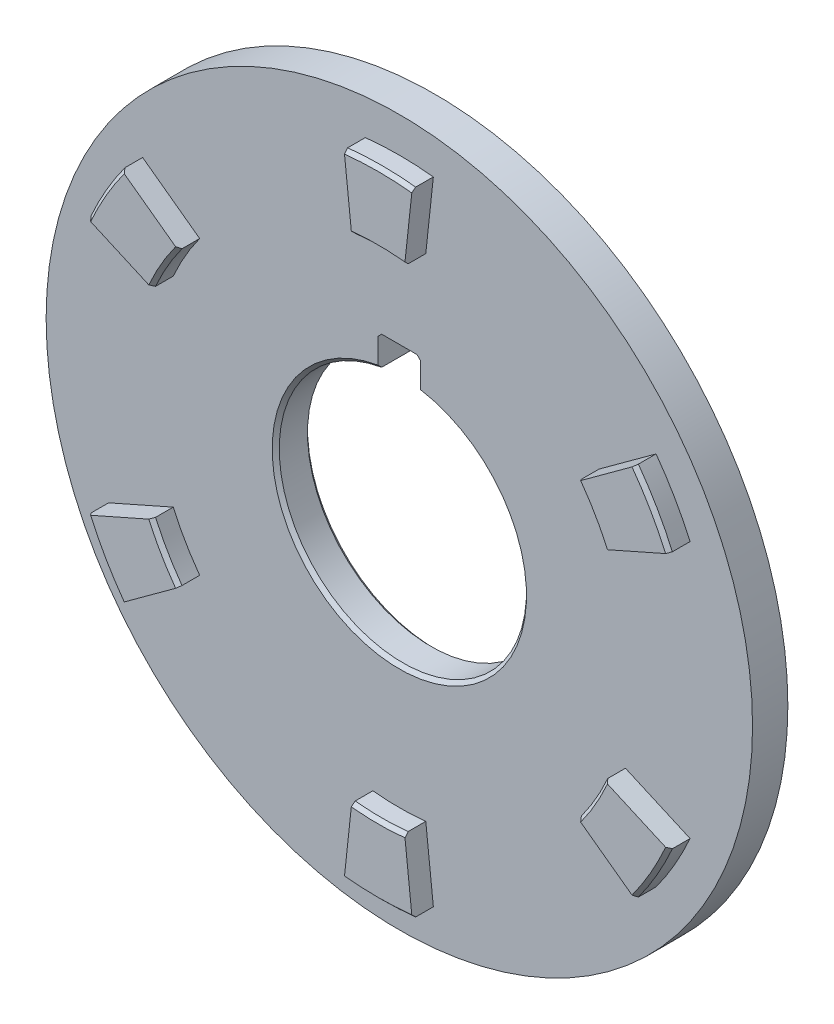
SolidWorks part; units mm, degrees
material "AISI 4340 Steel, normalized"
ref_plane "Front Plane" through (0, 0, 0) normal (0, 0, 1) x (1, 0, 0)
ref_plane "Top Plane" through (0, 0, 0) normal (0, 1, 0) x (1, 0, 0)
ref_plane "Right Plane" through (0, 0, 0) normal (1, 0, 0) x (0, 0, -1)
sketch "Sketch1" plane through (0, 0, 0) normal (0, 0, 1) x (1, 0, 0)
  circle A0 centre (0, 0) radius 100
  dimension "D1" = 200
extrude "Boss-Extrude1" add sketch "Sketch1" along normal mid plane 10
sketch "Sketch2" plane through (0, 0, 5) normal (0, 0, 1) x (1, 0, 0)
  line L0 (0, 0) -> (0, 43.6) construction
  line L1 (6, 34.4819) -> (6, 43.6)
  line L2 (-6, 34.4819) -> (-6, 43.6)
  line L4 (6, 43.6) -> (-6, 43.6)
  line L5 (6, 0) -> (6, 43.6) construction
  line L6 (-6, 0) -> (-6, 43.6) construction
  arc A3 (-6, 34.4819) -> (6, 34.4819) centre (0, 0) ccw
  dimension "D1" = 70
  dimension "D2" = 43.6
  dimension "D3" = 6
  dimension "D4" = 6
extrude "Cut-Extrude1" cut sketch "Sketch2" against normal through all
sketch "Sketch3" plane through (0, 0, 5) normal (0, 0, 1) x (1, 0, 0)
  line L0 (0, 0) -> (9.7713, 90.8031)
  line L1 (0, 0) -> (-9.729, 90.4104)
  line L2 (0, 0) -> (0, 95.1954) construction
  line L3 (0, 0) -> (83.5235, 36.9394)
  line L4 (0, 0) -> (73.4332, 53.6308)
  line L5 (0, 0) -> (73.7522, -53.8638)
  line L6 (0, 0) -> (83.1622, -36.7796)
  line L7 (0, 0) -> (-9.7713, -90.8031)
  line L8 (0, 0) -> (9.729, -90.4104)
  line L9 (0, 0) -> (-83.5235, -36.9394)
  line L10 (0, 0) -> (-73.4332, -53.6308)
  line L11 (0, 0) -> (-73.7522, 53.8638)
  line L12 (0, 0) -> (-83.1622, 36.7796)
  circle A0 centre (0, 0) radius 80 construction
  circle A1 centre (0, 0) radius 90
  circle A2 centre (0, 0) radius 70
  point P23 (0, 0)
  dimension "D1" = 10
  dimension "D3" = 160
  dimension "D4" = 12.284
  dimension "D2" = 10
  dimension "D5" = 6
extrude "Boss-Extrude3" add sketch "Sketch3" along normal blind 6 contours A2 L0 A1 L1 | A2 L11 A1 L12 | A2 L9 A1 L10 | A2 L7 A1 L8 | A2 L5 A1 L6 | A2 L3 A1 L4
chamfer "Chamfer1" distance 1 12 edges at (0, 70, 11) (0, 90, 11) (60.6218, 35, 11) (77.9423, 45, 11) (77.9423, -45, 11) (60.6218, -35, 11) (0, -70, 11) (0, -90, 11) (-77.9423, -45, 11) (-60.6218, -35, 11) (-77.9423, 45, 11) (-60.6218, 35, 11)
chamfer "Chamfer2" distance 1 2 edges at (0, -35, -5) (0, -35, 5)
chamfer "Chamfer3" distance 1 angle 45 2 edges at (6, 43.6, 0) (-6, 43.6, 0)
mirror "Mirror1" about plane through (0, 0, 0) normal (0, 0, 1) of "Chamfer1", "Boss-Extrude3"
